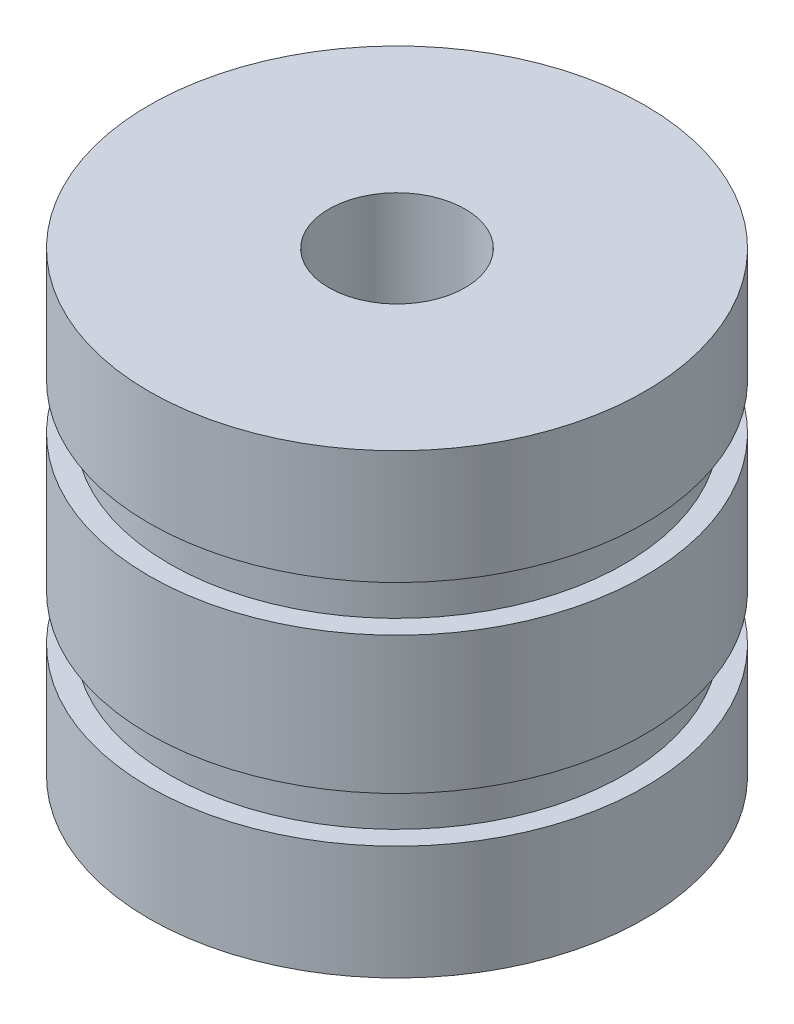
SolidWorks part; units mm, degrees
ref_plane "Front Plane" through (0, 0, 0) normal (0, 0, 1) x (1, 0, 0)
ref_plane "Top Plane" through (0, 0, 0) normal (0, 1, 0) x (1, 0, 0)
ref_plane "Right Plane" through (0, 0, 0) normal (1, 0, 0) x (0, 0, -1)
sketch "Sketch2" plane through (0, 0, 0) normal (0, 0, 1) x (1, 0, 0)
  line L0 (0, 48.8279) -> (0, -60.7812) construction
  line L1 (0, 0) -> (6, 0)
  line L2 (6, 0) -> (6, 2.7626)
  line L3 (6, 2.7626) -> (5.5, 2.7626)
  line L4 (5.5, 2.7626) -> (5.5, 3.8677)
  line L5 (5.5, 3.8677) -> (6, 3.8677)
  line L6 (6, 3.8677) -> (6, 7.1853)
  line L7 (6, 7.1853) -> (5.5, 7.1853)
  line L8 (5.5, 7.1853) -> (5.5, 8.2903)
  line L9 (5.5, 8.2903) -> (6, 8.2903)
  line L10 (6, 8.2903) -> (6, 11.0529)
  line L11 (6, 11.0529) -> (0, 11.0529)
  line L12 (0, 0) -> (0, 11.0529)
  point P5 (5.5, 3.3151)
  dimension "D1" = 5.5
  dimension "D2" = 6
revolve "Revolve1" add sketch "Sketch2" angle 360 about L0
sketch "Sketch3" plane through (0, 11.0529, 0) normal (0, 1, 0) x (1, 0, 0)
  circle A0 centre (0, 0) radius 2
hole_wizard "M4x0.7 Tapped Hole1" positions "3DSketch1" profile "Sketch4" tap size "M4x0.7" standard "ANSI Metric"
sketch3d "3DSketch1"
  point P0 (0, 11.0529, 0)
sketch "Sketch4" plane through (0, 11.0529, 0) normal (1, 0, 0) x (0, 0, 1)
  line L0 (0, 0) -> (0, 8.9914)
  line L1 (0, 8.9914) -> (1.65, 8)
  line L2 (1.65, 8) -> (1.65, 0)
  line L5 (1.65, 0) -> (0, 0)
  line L10 (0, 8.9914) -> (-1.65, 8) construction
  line L11 (0, -6.35) -> (0, 107.95) construction
  dimension "Tap Drill Dia." = 3.3
  dimension "Tap Drill Depth" = 8
  dimension "Drill Angle" = 118
cosmetic thread "Hole Thread1" parameters "D1"=8, "D2"=4
